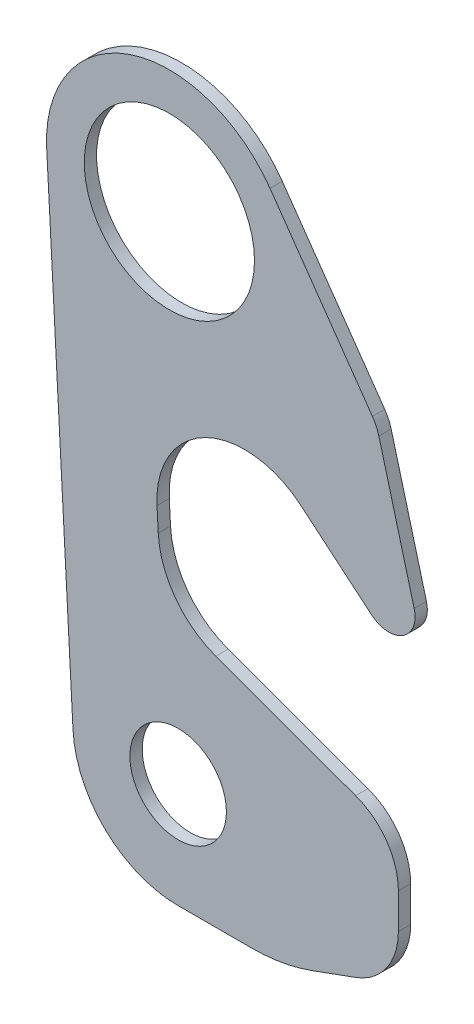
SolidWorks part; units mm, degrees
ref_plane "Plane1" through (0, 0, 0) normal (0, 0, 1) x (1, 0, 0)
ref_plane "Plane2" through (0, 0, 0) normal (0, 1, 0) x (1, 0, 0)
ref_plane "Plane3" through (0, 0, 0) normal (1, 0, 0) x (0, 0, -1)
sketch "Sketch1" plane through (0, 0, 0) normal (0, 0, 1) x (1, 0, 0)
  line L0 (-6.3436, -161.8338) -> (-7.0522, -148.6186)
  line L1 (5, -340) -> (46.9278, -340)
  line L2 (0, 0) -> (0, -86.5143) construction
  line L3 (-54.9139, -283.2127) -> (-69.8996, -3.7482)
  line L11 (57.3406, 40.1504) -> (115.7147, -43.2164)
  line L24 (75.0154, -107.6391) -> (115.3582, -141.4907)
  line L25 (139.4889, -126.1177) -> (119.384, -51.0854)
  line L28 (26.4837, -206.1412) -> (106.1547, -235.1391)
  line L30 (130.5, -290.0923) -> (130.5, -269.9077)
  line L31 (81.1299, -333.9693) -> (106.1547, -324.8609)
  line L32 (5, -280) -> (130.5, -280) construction
  circle A0 centre (0, 0) radius 48.5
  arc A1 (57.3406, 40.1504) -> (-69.8996, -3.7482) centre (0, 0) ccw
  arc A2 (26.4837, -206.1412) -> (-6.3436, -161.8338) centre (43.5847, -159.1565) cw
  arc A3 (-7.0522, -148.6186) -> (75.0154, -107.6391) centre (42.8761, -145.9413) cw
  arc A4 (46.9278, -340) -> (81.1299, -333.9693) centre (46.9278, -240) ccw
  arc A9 (-54.9139, -283.2127) -> (5, -340) centre (5, -280) ccw
  arc A15 (139.4889, -126.1177) -> (115.3582, -141.4907) centre (125, -130) cw
  arc A16 (119.384, -51.0854) -> (115.7147, -43.2164) centre (95.2359, -57.5558) ccw
  circle A23 centre (5, -280) radius 27.5
  arc A24 (130.5, -290.0923) -> (106.1547, -324.8609) centre (93.5, -290.0923) cw
  arc A25 (130.5, -269.9077) -> (106.1547, -235.1391) centre (93.5, -269.9077) ccw
  point P32 (130.5, -316)
  point P35 (130.5, -244)
  dimension "D4" = 410
  dimension "D5" = 25
  dimension "D6" = 35
  dimension "D7" = 55
  dimension "D10" = 50
  dimension "D11" = 50
  dimension "D8" = 15
  dimension "D18" = 145
  dimension "D19" = 37
  dimension "D13" = 210
  dimension "D3" = 60
  dimension "D17" = 5
  dimension "D23" = 97
  dimension "D24" = 70
  dimension "D25" = 55
  dimension "D26" = 100
  dimension "D9" = 20
  dimension "D12" = 20
  dimension "D14" = 20
  dimension "D15" = 125.5
  dimension "D16" = 72
  dimension "D2" = 280
  dimension "D22" = 35
extrude "Base-Extrude" add sketch "Sketch1" along normal blind 7
